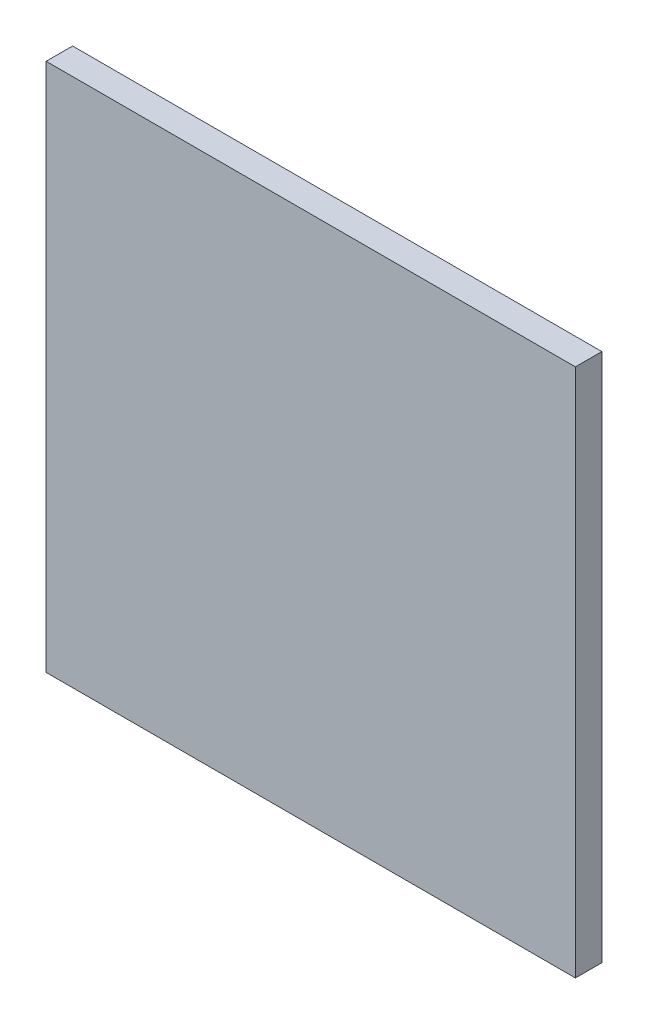
SolidWorks part; units mm, degrees
ref_plane "Front Plane" through (0, 0, 0) normal (0, 0, 1) x (1, 0, 0)
ref_plane "Top Plane" through (0, 0, 0) normal (0, 1, 0) x (1, 0, 0)
ref_plane "Right Plane" through (0, 0, 0) normal (1, 0, 0) x (0, 0, -1)
sketch "Sketch5" plane through (0, 0, 0) normal (0, 0, 1) x (1, 0, 0)
  line L1 (0, 0) -> (10000, 0)
  line L2 (0, 0) -> (0, 10000)
  line L3 (0, 10000) -> (10000, 10000)
  line L4 (10000, 0) -> (10000, 10000)
  dimension "D1" = 10000
  dimension "D2" = 10000
extrude "Boss-Extrude2" add sketch "Sketch5" against normal blind 500
